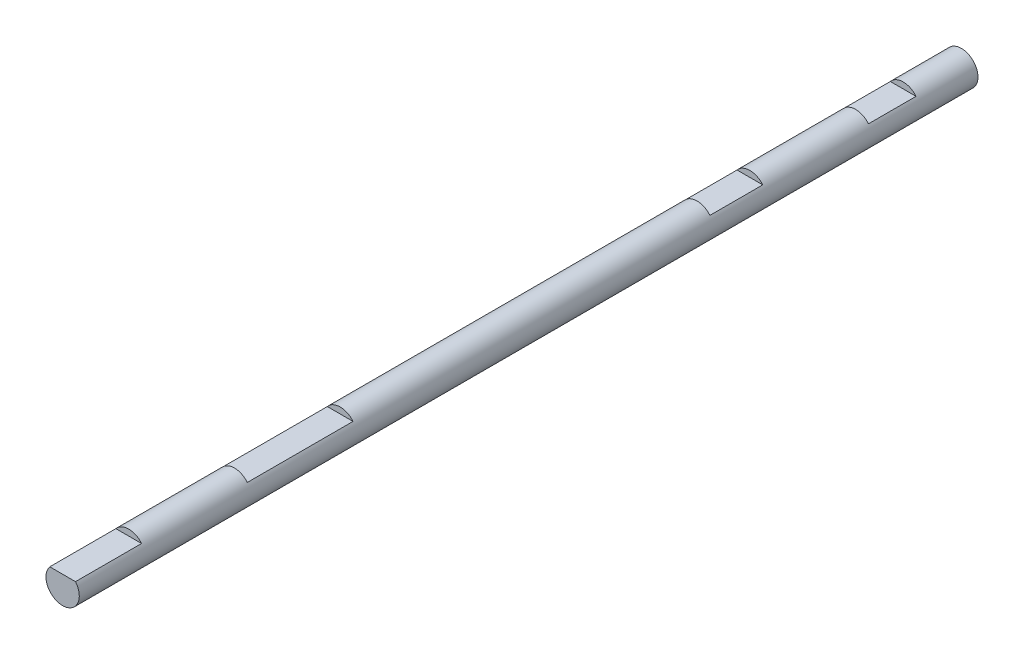
SolidWorks part; units mm, degrees
material "Chrome Stainless Steel"
ref_plane "Front Plane" through (0, 0, 0) normal (0, 0, 1) x (1, 0, 0)
ref_plane "Top Plane" through (0, 0, 0) normal (0, 1, 0) x (1, 0, 0)
ref_plane "Right Plane" through (0, 0, 0) normal (1, 0, 0) x (0, 0, -1)
sketch "Sketch1" plane through (0, 0, 0) normal (0, 0, 1) x (1, 0, 0)
  circle A0 centre (0, 0) radius 4
  dimension "D1" = 8
extrude "Boss-Extrude1" add sketch "Sketch1" along normal blind 215.9
sketch "Sketch2" plane through (0, 0, 0) normal (1, 0, 0) x (0, 0, -1)
  line L1 (-215.9, 4) -> (-200.025, 4)
  line L2 (-215.9, 4) -> (-215.9, 2.54)
  line L3 (-215.9, 2.54) -> (-200.025, 2.54)
  line L4 (-200.025, 4) -> (-200.025, 2.54)
  line L5 (0, 0) -> (-248.0609, 0) construction
  line L6 (0, 4) -> (-215.9, 4) construction
  line L7 (-174.625, 4) -> (-149.225, 4)
  line L8 (-174.625, 4) -> (-174.625, 2.54)
  line L9 (-174.625, 2.54) -> (-149.225, 2.54)
  line L10 (-149.225, 4) -> (-149.225, 2.54)
  line L11 (-215.9, 4) -> (-215.9, -4) construction
  line L12 (-215.9, 2.54) -> (-25.4, 2.54) construction
  line L13 (0, -4) -> (0, 4) construction
  line L14 (-25.4, 2.54) -> (0, 2.54) construction
  line L19 (-63.5, 4) -> (-50.8, 4)
  line L20 (-63.5, 4) -> (-63.5, 2.54)
  line L21 (-63.5, 2.54) -> (-50.8, 2.54)
  line L22 (-50.8, 4) -> (-50.8, 2.54)
  line L24 (-25.4, 4) -> (-25.4, 2.54)
  line L28 (-25.4, 4) -> (-13.97, 4)
  line L29 (-25.4, 4) -> (-25.4, 2.54)
  line L30 (-25.4, 2.54) -> (-13.97, 2.54)
  line L31 (-13.97, 4) -> (-13.97, 2.54)
  point P27 (-63.5, 3.27)
  dimension "D1" = 15.875
  dimension "D2" = 2.54
  dimension "D3" = 41.275
  dimension "D4" = 25.4
  dimension "D7" = 152.4
  dimension "D8" = 12.7
  dimension "D9" = 190.5
  dimension "D10" = 11.43
extrude "Cut-Extrude1" cut sketch "Sketch2" against normal mid plane 12.7 contours L22 L19 L20 L21 | L10 L7 L8 L9 | L4 L1 L2 L3 | L29 L28 L31 L30
